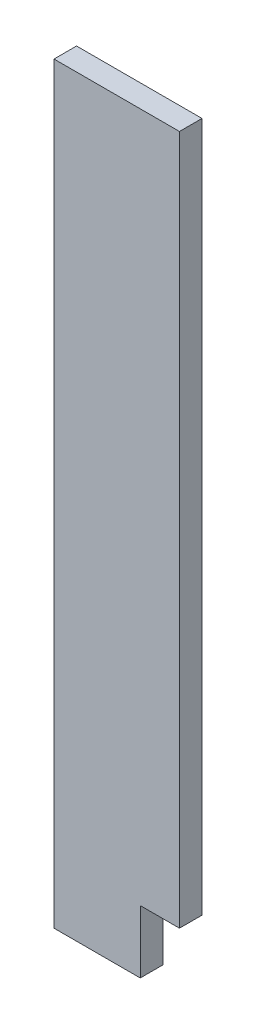
SolidWorks part; units mm, degrees
material "Pine"
ref_plane "Front Plane" through (0, 0, 0) normal (0, 0, 1) x (1, 0, 0)
ref_plane "Top Plane" through (0, 0, 0) normal (0, 1, 0) x (1, 0, 0)
ref_plane "Right Plane" through (0, 0, 0) normal (1, 0, 0) x (0, 0, -1)
sketch "Sketch1" plane through (0, 0, 0) normal (0, 0, 1) x (1, 0, 0)
  line L1 (-52.3819, 110.7189) -> (49.2181, 110.7189)
  line L2 (-52.3819, 110.7189) -> (-52.3819, -498.8811)
  line L3 (-52.3819, -498.8811) -> (49.2181, -498.8811)
  line L4 (49.2181, 110.7189) -> (49.2181, -498.8811)
  dimension "D1" = 101.6
  dimension "D2" = 609.6
extrude "Boss-Extrude1" add sketch "Sketch1" along normal blind 18.2562
sketch "Sketch2" plane through (0, 0, 18.2562) normal (0, 0, 1) x (1, 0, 0)
  line L1 (49.2181, -498.8811) -> (17.4681, -498.8811)
  line L2 (49.2181, -498.8811) -> (49.2181, -448.0811)
  line L3 (49.2181, -448.0811) -> (17.4681, -448.0811)
  line L4 (17.4681, -498.8811) -> (17.4681, -448.0811)
  dimension "D1" = 31.75
  dimension "D2" = 50.8
extrude "Cut-Extrude1" cut sketch "Sketch2" against normal through all
